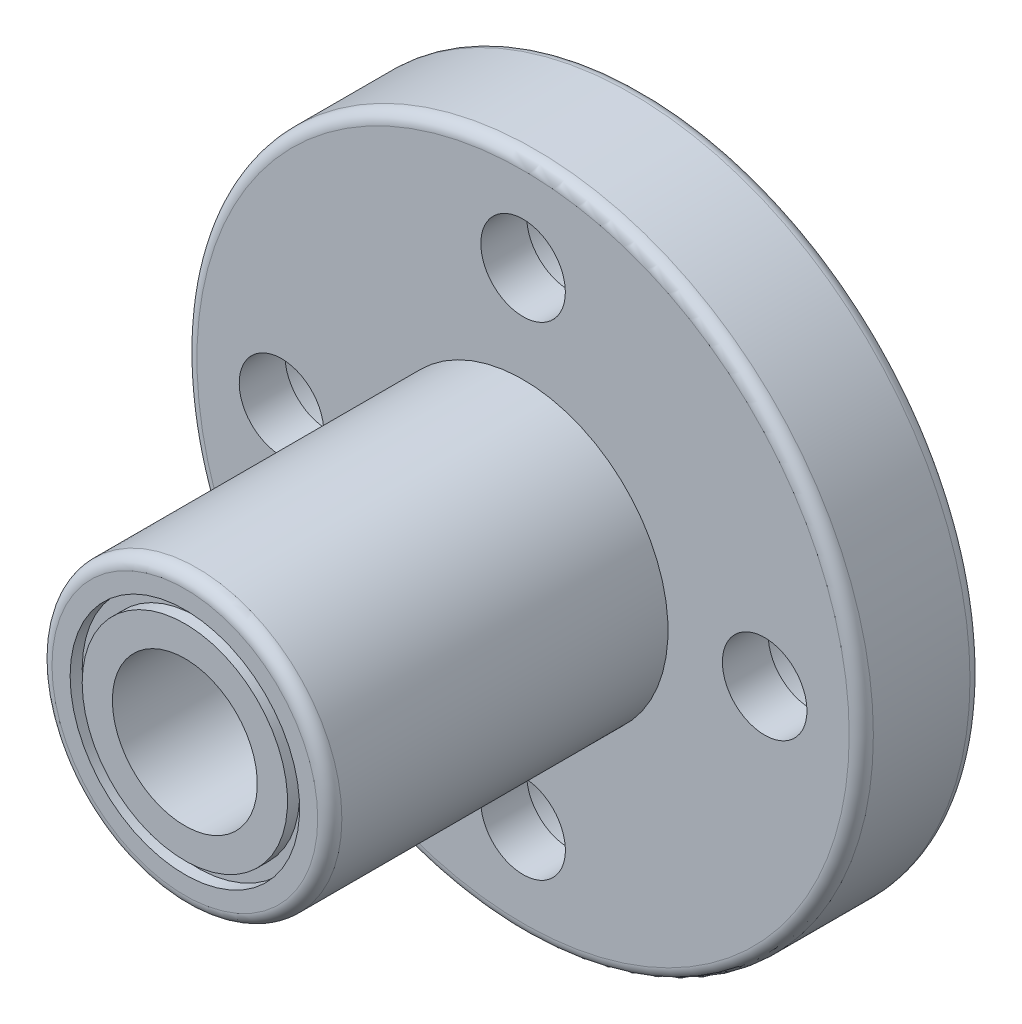
SolidWorks part; units mm, degrees
material "AISI 316 Отожженная нержавеющая сталь. полоса (SS)"
ref_plane "Plano frontal" through (0, 0, 0) normal (0, 0, 1) x (1, 0, 0)
ref_plane "Plano superior" through (0, 0, 0) normal (0, 1, 0) x (1, 0, 0)
ref_plane "Plano direito" through (0, 0, 0) normal (1, 0, 0) x (0, 0, -1)
sketch "Esboço1" plane through (0, 0, 0) normal (-1, 0, 0) x (0, 0, -1)
  line L0 (0, 3) -> (0, 4.25)
  line L1 (0, 14) -> (-5, 14)
  line L2 (-5, 14) -> (-5, 6)
  line L3 (-5, 6) -> (-19, 6)
  line L4 (-19, 6) -> (-19, 4.75)
  line L5 (-19, 3) -> (0, 3)
  line L6 (0, 0) -> (-226.2321, 0) construction
  line L7 (-19, 4.75) -> (-18.5, 4.75)
  line L8 (-18.5, 4.75) -> (-18.5, 4.25)
  line L9 (-18.5, 4.25) -> (-19, 4.25)
  line L10 (0, 6) -> (-0.5, 6)
  line L11 (-0.5, 6) -> (-0.5, 5.5)
  line L12 (-0.5, 5.5) -> (0, 5.5)
  line L13 (0, 6) -> (0, 14)
  line L14 (-19, 4.25) -> (-19, 3)
  line L15 (0, 4.75) -> (-0.5, 4.75)
  line L16 (-0.5, 4.75) -> (-0.5, 4.25)
  line L17 (-0.5, 4.25) -> (0, 4.25)
  line L18 (0, 4.75) -> (0, 5.5)
  dimension "D1" = 19
  dimension "D2" = 12
  dimension "D3" = 6
  dimension "D4" = 28
  dimension "D5" = 5
  dimension "D6" = 0.5
  dimension "D7" = 0.5
  dimension "D8" = 0.5
  dimension "D9" = 0.5
  dimension "D10" = 0.5
  dimension "D11" = 0.5
revolve "Revolução1" add sketch "Esboço1" angle 360 about L6
sketch "Esboço5" plane through (0, 0, 0) normal (1, 0, 0) x (0, 0, -1)
  line L0 (0, 13) -> (-3.1, 13)
  line L1 (0, -14) -> (0, 14) construction
  line L2 (-3.1, 13) -> (-3.1, 11.75)
  line L3 (-3.1, 11.75) -> (-5, 11.75)
  line L4 (-5, 14) -> (-5, -14) construction
  line L5 (-5, 11.75) -> (-5, 10)
  line L6 (-5, 10) -> (0, 10)
  line L7 (0, 10) -> (0, 13)
  line L8 (0, 10) -> (2.2336, 10) construction
  line L9 (0, 0) -> (9.7959, 0) construction
  dimension "D1" = 6
  dimension "D2" = 3.5
  dimension "D3" = 3.1
  dimension "D4" = 20
revolve "Corte-Revolução1" cut sketch "Esboço5" angle 360 about L8
pattern_circular "PadrãoCircular1" count 4 over 360 about axis through (0, 0, 0) along (0, 0, 1) of "Corte-Revolução1"
fillet "Filete1" radius 0.5 3 edges at (-14, 0, 0) (-14, 0, 5) (-6, 0, 19)
